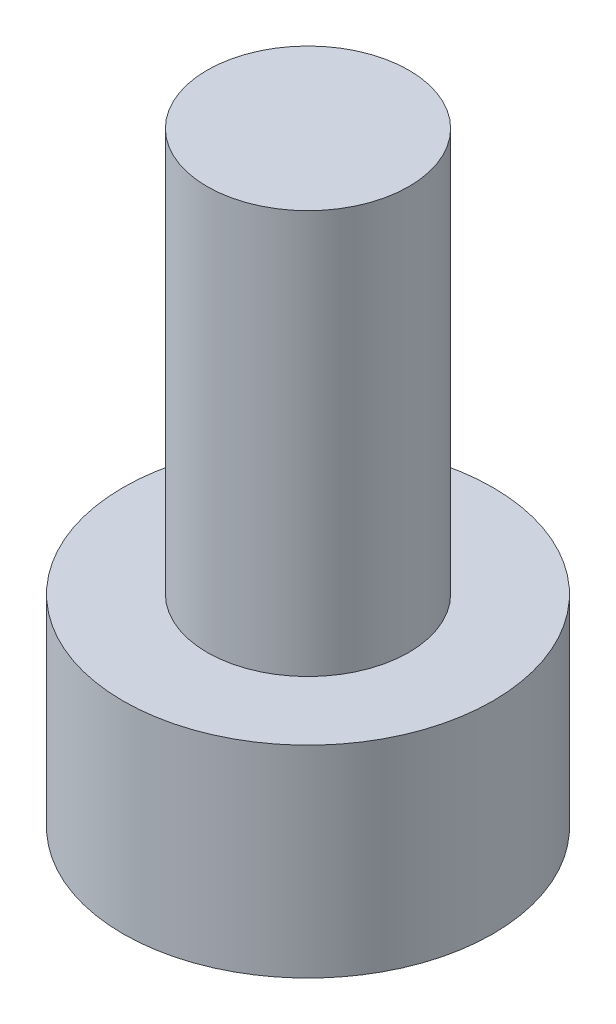
SolidWorks part; units mm, degrees
material "AISI 304"
ref_plane "前视基准面" through (0, 0, 0) normal (0, 0, 1) x (1, 0, 0)
ref_plane "上视基准面" through (0, 0, 0) normal (0, 1, 0) x (1, 0, 0)
ref_plane "右视基准面" through (0, 0, 0) normal (1, 0, 0) x (0, 0, -1)
other "Configuration Table"
sketch "草图1" plane through (0, 0, 0) normal (0, 1, 0) x (1, 0, 0)
  circle A0 centre (0, 0) radius 2.75
  dimension "D1" = 5.5
extrude "凸台-拉伸1" add sketch "草图1" along normal blind 3
sketch "草图2" plane through (0, 3, 0) normal (0, 1, 0) x (1, 0, 0)
  circle A0 centre (0, 0) radius 1.5
  dimension "D1" = 3
extrude "凸台-拉伸2" add sketch "草图2" along normal blind 6
sketch "草图3" plane through (0, 0, 0) normal (0, -1, 0) x (1, 0, 0)
  line L1 (0.7436, 1.2907) -> (-0.746, 1.2893)
  line L2 (-0.746, 1.2893) -> (-1.4896, -0.0014)
  line L3 (-1.4896, -0.0014) -> (-0.7436, -1.2907)
  line L4 (-0.7436, -1.2907) -> (0.746, -1.2893)
  line L5 (0.746, -1.2893) -> (1.4896, 0.0014)
  line L6 (1.4896, 0.0014) -> (0.7436, 1.2907)
  circle A0 centre (0, 0) radius 1.29 construction
  dimension "D1" = 2.58
extrude "切除-拉伸1" cut sketch "草图3" against normal blind 1.3
